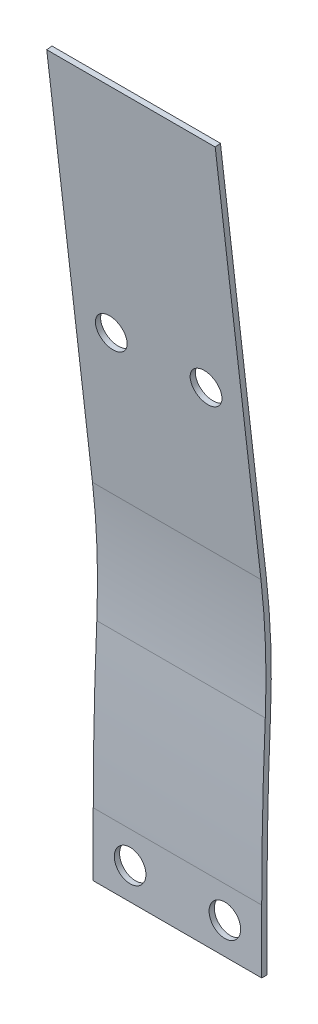
SolidWorks part; units mm, degrees
ref_plane "Front Plane" through (0, 0, 0) normal (0, 0, 1) x (1, 0, 0)
ref_plane "Top Plane" through (0, 0, 0) normal (0, 1, 0) x (1, 0, 0)
ref_plane "Right Plane" through (0, 0, 0) normal (1, 0, 0) x (0, 0, -1)
sketch "Sketch1" plane through (0, 0, 0) normal (0, 0, 1) x (1, 0, 0)
  line L0 (-4.5, 0) -> (4.5, 0) construction
  line L1 (-8, 3) -> (8, 3)
  line L2 (-8, 3) -> (-8, -3)
  line L3 (-8, -3) -> (8, -3)
  line L4 (8, 3) -> (8, -3)
  line L5 (4.5, 0) -> (8, 0) construction
  line L6 (0, 0) -> (0, -3) construction
  circle A0 centre (-4.5, 0) radius 1.5
  circle A1 centre (4.5, 0) radius 1.5
  point P8 (0, 0)
  dimension "D4" = 3
  dimension "D1" = 9
  dimension "D2" = 6
  dimension "D3" = 16
extrude "Boss-Extrude1" add sketch "Sketch1" along normal blind 0.5
sketch "Sketch2" plane through (-8, 0, 0) normal (-1, 0, 0) x (0, 0, 1)
  line L0 (0.5724, 29.8072) -> (4.0029, 59.6104)
  line L1 (0.0756, 29.8644) -> (1.6669, 43.6883)
  line L2 (0, 3) -> (0, -3) construction
  line L3 (0, 3) -> (0, -3) construction
  line L4 (0.5, 3) -> (0.5, -3) construction
  line L5 (0.5, 3) -> (0.5, -3) construction
  line L6 (1.915, 45.8437) -> (1.6669, 43.6883)
  line L7 (1.915, 45.8437) -> (3.5062, 59.6676)
  line L8 (3.5062, 59.6676) -> (4.0029, 59.6104)
  line L10 (0.5, 3) -> (0, 3) construction
  line L11 (0.5, 3) -> (0, 3) construction
  line L13 (0.5724, 29.8072) -> (2.1636, 43.6312) construction
  arc A0 (0.0756, 29.8644) -> (-0.3355, 18.1982) centre (73.2048, 21.4467) ccw
  arc A1 (-0.3355, 18.1982) -> (0, 3) centre (-344.3902, 3) cw
  arc A2 (0.5724, 29.8072) -> (0.164, 18.2202) centre (73.2048, 21.4467) ccw
  arc A3 (0.164, 18.2202) -> (0.5, 3) centre (-344.3902, 3) cw
  line M4 (0.5, 3) -> (0, 3)
  dimension "D1" = 0.5
extrude "Boss-Extrude2" add sketch "Sketch2" against normal up to surface (16 mm away) contours A3 A2 L0 L8 L7 L6 L1 A0 A1 M4 up to face at (8, 0, 0.25)
sketch "Sketch3" plane through (0, 0.3819, -3.318) normal (0, 0.1144, -0.9934) x (-1, 0, 0)
  line L0 (8, 44.6772) -> (4.5, 44.6772) construction
  line L1 (8, 29.6772) -> (8, 59.6772) construction
  line L2 (4.5, 44.6772) -> (-4.5, 44.6772) construction
  circle A0 centre (-4.5, 44.6772) radius 1.5
  circle A1 centre (4.5, 44.6772) radius 1.5
  point P4 (0, 44.6772)
  dimension "D2" = 3
  dimension "D1" = 9
extrude "Cut-Extrude1" cut sketch "Sketch3" against normal through all
sketch "Sketch4" plane through (0, 0.3819, -3.318) normal (0, 0.1144, -0.9934) x (-1, 0, 0)
  line L1 (-8, 59.6772) -> (8, 59.6772)
  line L2 (-8, 59.6772) -> (-8, 67.6772)
  line L3 (-8, 67.6772) -> (8, 67.6772)
  line L4 (8, 59.6772) -> (8, 67.6772)
  dimension "D1" = 8
extrude "Boss-Extrude3" add sketch "Sketch4" against normal up to surface (0.5 mm away) up to face at (4.5, 43.2187, 2.1161)
